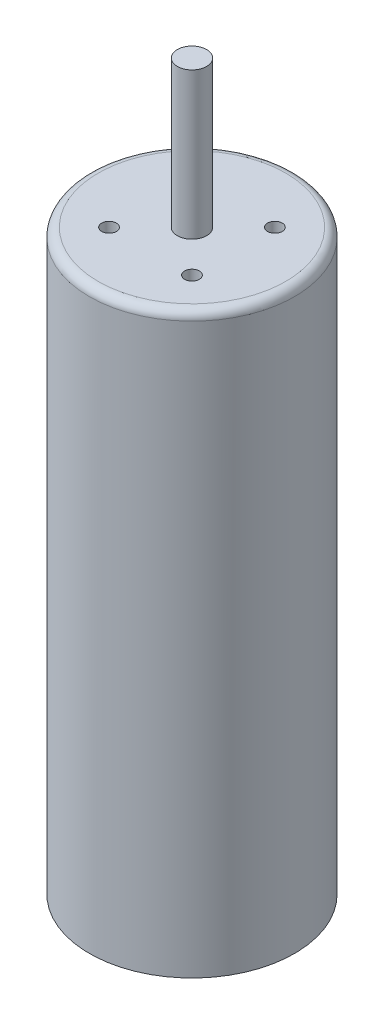
SolidWorks part; units mm, degrees
ref_plane "前视基准面" through (0, 0, 0) normal (0, 0, 1) x (1, 0, 0)
ref_plane "上视基准面" through (0, 0, 0) normal (0, 1, 0) x (1, 0, 0)
ref_plane "右视基准面" through (0, 0, 0) normal (1, 0, 0) x (0, 0, -1)
sketch "草图1" plane through (0, 0, 0) normal (0, 1, 0) x (1, 0, 0)
  circle A0 centre (0, 0) radius 3.5
  dimension "D1" = 7
extrude "凸台-拉伸1" add sketch "草图1" along normal blind 20
sketch "草图2" plane through (0, 20, 0) normal (0, 1, 0) x (1, 0, 0)
  circle A0 centre (0, 0) radius 0.5
extrude "凸台-拉伸2" add sketch "草图2" along normal blind 5
fillet "圆角1" radius 0.3 1 edges at (0, 20, 3.5)
sketch "草图3" plane through (0, 20, 0) normal (0, 1, 0) x (1, 0, 0)
  line L0 (-3.2, 0) -> (3.2, 0) construction
  line L1 (0, 3.2) -> (0, -3.2) construction
  line L2 (-2.2627, 2.2627) -> (2.2627, -2.2627) construction
  line L3 (2.2627, 2.2627) -> (-2.2627, -2.2627) construction
  circle A0 centre (0, 0) radius 3.2 construction
  circle A1 centre (-1.4142, 1.4142) radius 0.25
  circle A2 centre (1.4142, 1.4142) radius 0.25
  circle A3 centre (1.4142, -1.4142) radius 0.25
  circle A4 centre (-1.4142, -1.4142) radius 0.25
  point P23 (0, 0)
  dimension "D3" = 0.5
  dimension "D1" = 45
  dimension "D2" = 45
  dimension "D4" = 2
  dimension "D5" = 4
extrude "切除-拉伸1" cut sketch "草图3" against normal blind 5
sketch "草图4" plane through (0, 0, 0) normal (0, -1, 0) x (1, 0, 0)
  circle A0 centre (0, 0) radius 3
  dimension "D1" = 6
extrude "切除-拉伸2" cut sketch "草图4" against normal blind 0.3 flip side to cut
sketch "草图5" plane through (0, 0, 0) normal (0, -1, 0) x (1, 0, 0)
  circle A0 centre (0, 0) radius 0.5
  dimension "D1" = 1
extrude "切除-拉伸3" cut sketch "草图5" against normal blind 0.3
